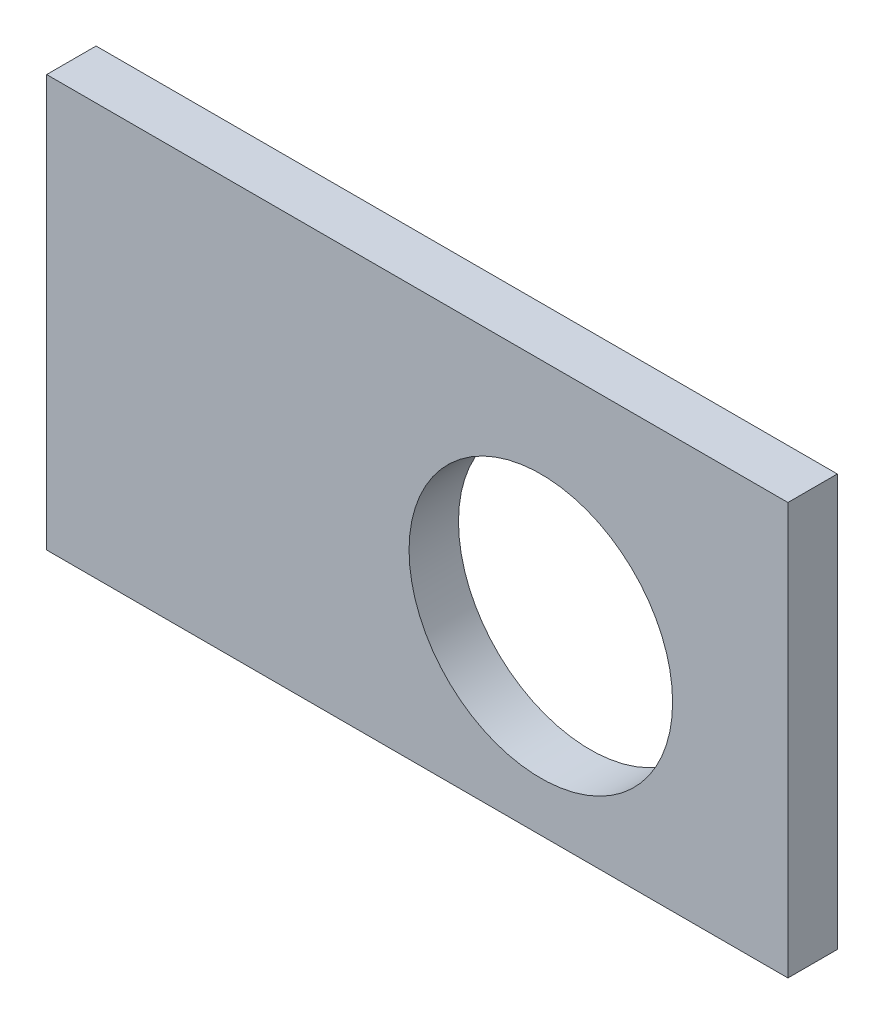
SolidWorks part; units mm, degrees
ref_plane "Front Plane" through (0, 0, 0) normal (0, 0, 1) x (1, 0, 0)
ref_plane "Top Plane" through (0, 0, 0) normal (0, 1, 0) x (1, 0, 0)
ref_plane "Right Plane" through (0, 0, 0) normal (1, 0, 0) x (0, 0, -1)
sketch "Sketch1" plane through (0, 0, 0) normal (0, 0, 1) x (1, 0, 0)
  line L1 (0, 0) -> (90, 0)
  line L2 (0, 0) -> (0, 50)
  line L3 (0, 50) -> (90, 50)
  line L4 (90, 0) -> (90, 50)
  circle A0 centre (60, 22) radius 16
  dimension "D3" = 32
  dimension "D1" = 50
  dimension "D2" = 90
  dimension "D4" = 60
  dimension "D5" = 28
extrude "Boss-Extrude1" add sketch "Sketch1" along normal blind 6
